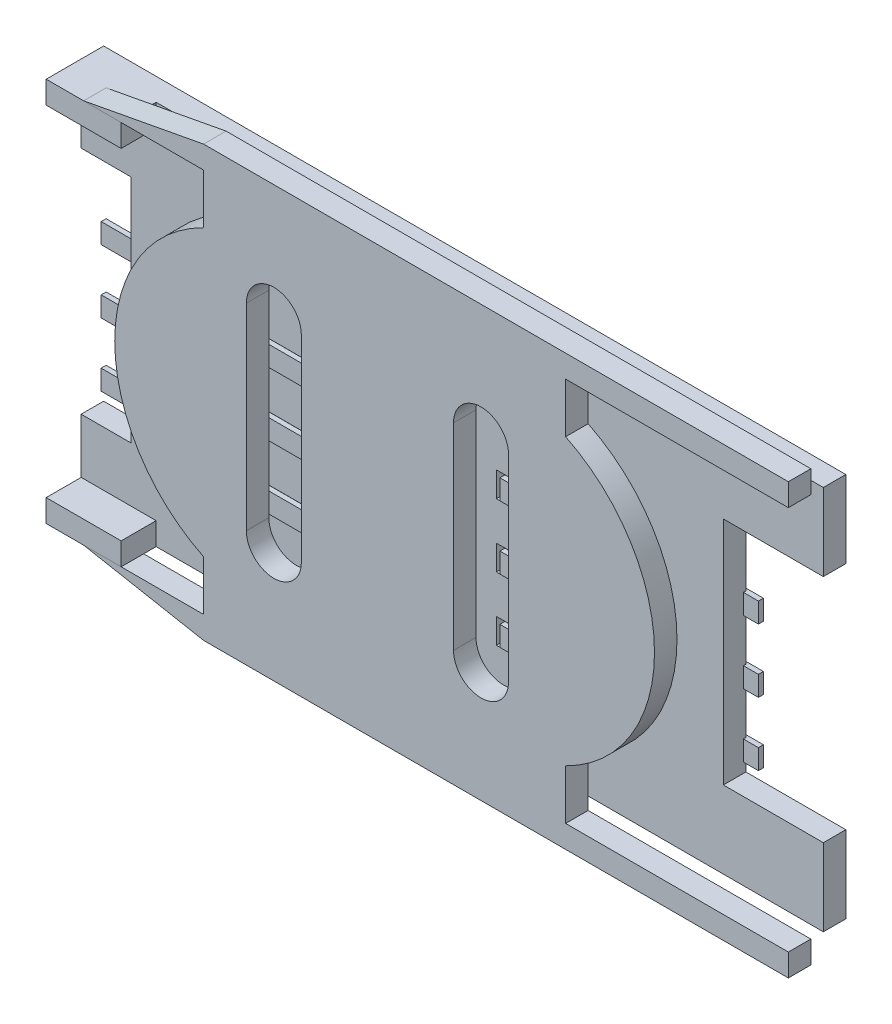
SolidWorks part; units mm, degrees
ref_plane "Front Plane" through (0, 0, 0) normal (0, 0, 1) x (1, 0, 0)
ref_plane "Top Plane" through (0, 0, 0) normal (0, 1, 0) x (1, 0, 0)
ref_plane "Right Plane" through (0, 0, 0) normal (1, 0, 0) x (0, 0, -1)
sketch "Sketch1" plane through (0, 0, 0) normal (0, 0, 1) x (1, 0, 0)
  line L0 (29.7, 12.31) -> (29.7, 15.4)
  line L1 (0, 0) -> (29.7, 0)
  line L2 (0, 0) -> (0, 3.09)
  line L3 (0, 15.4) -> (29.7, 15.4)
  line L4 (29.7, 0) -> (29.7, 3.09)
  line L5 (0, 12.31) -> (2, 12.31)
  line L6 (14.85, 15.4) -> (14.85, 0) construction
  line L7 (0, 3.09) -> (2, 3.09)
  line L8 (2, 12.31) -> (2, 3.09)
  line L9 (29.7, 12.31) -> (25.7, 12.31)
  line L10 (0, 12.31) -> (0, 15.4)
  line L11 (29.7, 3.09) -> (25.7, 3.09)
  line L12 (25.7, 12.31) -> (25.7, 3.09)
  line L13 (-2.6552, 7.7) -> (34.3923, 7.7) construction
  line L14 (-1.5692, 3.89) -> (31.5309, 3.89) construction
  line L15 (3.3098, 4.39) -> (9.6859, 4.39)
  line L16 (3.3098, 4.39) -> (3.3098, 3.39)
  line L17 (3.3098, 3.39) -> (9.6859, 3.39)
  line L18 (9.6859, 4.39) -> (9.6859, 3.39)
  line L19 (16.6164, 4.39) -> (22.3271, 4.39)
  line L20 (16.6164, 4.39) -> (16.6164, 3.39)
  line L21 (16.6164, 3.39) -> (22.3271, 3.39)
  line L22 (22.3271, 4.39) -> (22.3271, 3.39)
  line L23 (3.3098, 6.93) -> (9.6859, 6.93)
  line L24 (3.3098, 6.93) -> (3.3098, 5.93)
  line L25 (3.3098, 5.93) -> (9.6859, 5.93)
  line L26 (9.6859, 6.93) -> (9.6859, 5.93)
  line L27 (16.6164, 6.93) -> (22.3271, 6.93)
  line L28 (16.6164, 6.93) -> (16.6164, 5.93)
  line L29 (16.6164, 5.93) -> (22.3271, 5.93)
  line L30 (22.3271, 6.93) -> (22.3271, 5.93)
  line L31 (3.3098, 9.47) -> (9.6859, 9.47)
  line L32 (3.3098, 9.47) -> (3.3098, 8.47)
  line L33 (3.3098, 8.47) -> (9.6859, 8.47)
  line L34 (9.6859, 9.47) -> (9.6859, 8.47)
  line L35 (16.6164, 9.47) -> (22.3271, 9.47)
  line L36 (16.6164, 9.47) -> (16.6164, 8.47)
  line L37 (16.6164, 8.47) -> (22.3271, 8.47)
  line L38 (22.3271, 9.47) -> (22.3271, 8.47)
  point P17 (14.85, 7.7)
  point P18 (2, 7.7)
  point P19 (25.7, 7.7)
  point P30 (9.6859, 3.89)
  point P31 (22.3271, 3.89)
  dimension "D1" = 29.7
  dimension "D2" = 15.4
  dimension "D3" = 9.22
  dimension "D4" = 9.22
  dimension "D5" = 2
  dimension "D6" = 4
  dimension "D7" = 1
  dimension "D8" = 1
  dimension "D9" = 0.8
  dimension "D10" = 3
extrude "Boss-Extrude1" add sketch "Sketch1" along normal blind 0.9
ref_plane "Plane1" through (0, 0, 2.3) normal (0, 0, -1) x (-1, 0, 0)
sketch "Sketch4" plane through (0, 0, 0.9) normal (0, 0, 1) x (1, 0, 0)
  line L0 (25.7, 12.31) -> (25.7, 3.09) construction
  line L1 (0, 15.4) -> (3, 15.4)
  line L2 (0, 15.4) -> (0, 14.5)
  line L3 (0, 14.5) -> (3, 14.5)
  line L4 (3, 15.4) -> (3, 14.5)
  line L5 (25.7, 7.7) -> (2, 7.7) construction
  line L6 (2, 12.31) -> (2, 3.09) construction
  line L7 (3, 0) -> (3, 0.9)
  line L8 (0, 0.9) -> (3, 0.9)
  line L9 (0, 0) -> (0, 0.9)
  line L10 (0, 0) -> (3, 0)
  dimension "D1" = 3
  dimension "D2" = 0.9
extrude "Boss-Extrude3" add sketch "Sketch4" along normal up to surface (1.4 mm away) up to plane "Plane1"
sketch "Sketch5" plane through (0, 0, 2.3) normal (0, 0, -1) x (-1, 0, 0)
  line L0 (-25.7, 12.31) -> (-25.7, 3.09) construction
  line L1 (-6.2994, -0.9) -> (-29.7, -0.9)
  line L2 (-6.2994, 0) -> (-6.2994, 1.9977)
  line L3 (-6.2994, 16.3) -> (-29.7, 16.3)
  line L4 (-29.7, -0.9) -> (-29.7, 0)
  line L5 (3.826, 7.7) -> (-37.3942, 7.7) construction
  line L6 (-6.2994, 16.3) -> (-1.5, 15.4)
  line L7 (0, 15.4) -> (-3, 15.4) construction
  line L8 (-1.5, 15.4) -> (-6.2994, 15.4)
  line L9 (-29.7, 15.4) -> (-3, 15.4) construction
  line L10 (-20.7876, 15.4) -> (-20.7876, 13.4023)
  line L11 (-20.7876, 15.4) -> (-29.7, 15.4)
  line L12 (-6.2994, 13.4023) -> (-6.2994, 15.4)
  line L13 (-20.7876, 1.9977) -> (-20.7876, 0)
  line L14 (-20.7876, 0) -> (-29.7, 0)
  line L15 (-3, 0) -> (-29.7, 0) construction
  line L16 (-29.7, 15.4) -> (-29.7, 16.3)
  line L17 (-1.5, 0) -> (-6.2994, 0)
  line L18 (-6.2994, -0.9) -> (-1.5, 0)
  arc A0 (-6.2994, 1.9977) -> (-6.2994, 13.4023) centre (-9.0934, 7.7) ccw
  arc A1 (-20.7876, 13.4023) -> (-20.7876, 1.9977) centre (-17.9936, 7.7) ccw
  point P10 (-25.7, 7.7)
  dimension "D2" = 6.35
  dimension "D4" = 6.35
  dimension "D1" = 17.2
extrude "Boss-Extrude4" add sketch "Sketch5" along normal blind 0.9 separate body
sketch "Sketch6" plane through (0, 0, 2.3) normal (0, 0, 1) x (1, 0, 0)
  line L0 (2.7434, 7.7) -> (24.3436, 7.7) construction
  line L1 (16.3018, 11.6434) -> (16.3018, 3.7566)
  line L2 (8.011, 11.6434) -> (8.011, 3.7566)
  line L3 (18.5015, 3.7566) -> (18.5015, 11.6434)
  line L4 (10.2107, 3.7566) -> (10.2107, 11.6434)
  arc A0 (6.2994, 13.4023) -> (6.2994, 1.9977) centre (9.0934, 7.7) ccw construction
  arc A1 (20.7876, 1.9977) -> (20.7876, 13.4023) centre (17.9936, 7.7) ccw construction
  arc A2 (18.5015, 11.6434) -> (16.3018, 11.6434) centre (17.4016, 11.6434) ccw
  arc A3 (18.5015, 3.7566) -> (16.3018, 3.7566) centre (17.4016, 3.7566) cw
  arc A4 (10.2107, 3.7566) -> (8.011, 3.7566) centre (9.1108, 3.7566) cw
  arc A5 (10.2107, 11.6434) -> (8.011, 11.6434) centre (9.1108, 11.6434) ccw
extrude "Cut-Extrude1" cut sketch "Sketch6" against normal up to surface (0.9 mm away) up to face at (15.1717, 7.7, 1.4)
ref_plane "Plane2" through (0, 3.8853, 0) normal (0, 1, 0) x (1, 0, 0)
sketch "Sketch7" plane through (0, 3.8853, 0) normal (0, 1, 0) x (1, 0, 0)
  line L0 (0, 0) -> (5.842, 0)
  line L1 (29.7, 0) -> (0, 0) construction
  line L2 (29.7, -0.9) -> (3, -0.9) construction
  line L3 (5.842, -0.9) -> (5.842, 0)
  line L4 (7.082, -0.9) -> (9.4442, -0.9)
  line L5 (9.6859, -0.45) -> (16.6164, -0.45) construction
  line L6 (9.6859, -0.9) -> (9.6859, 0) construction
  line L7 (16.6164, -0.9) -> (16.6164, 0) construction
  line L8 (16.6164, -0.45) -> (13.1512, -0.45) construction
  line L9 (13.1512, -0.45) -> (13.1512, -0.9) construction
  line L10 (3, -0.9) -> (29.7, -0.9) construction
  line L11 (19.2203, -0.9) -> (16.8581, -0.9)
  line L12 (20.4603, -0.9) -> (20.4603, 0)
  line L13 (26.3023, 0) -> (20.4603, 0)
  arc A0 (5.842, -0.9) -> (7.082, -0.9) centre (6.462, -0.9) ccw
  arc A1 (20.4603, -0.9) -> (19.2203, -0.9) centre (19.8403, -0.9) cw
  dimension "D1" = 0.62
  dimension "D2" = 5.842
  dimension "D3" = 2.3622
extrude "Extrude-Thin1" add sketch "Sketch7" along normal mid plane 0.8 separate body thin thin type mid plane wall 0.2
pattern_linear "LPattern1" count 3 spacing 2.54 along (0, 1, 0) of "Extrude-Thin1"
